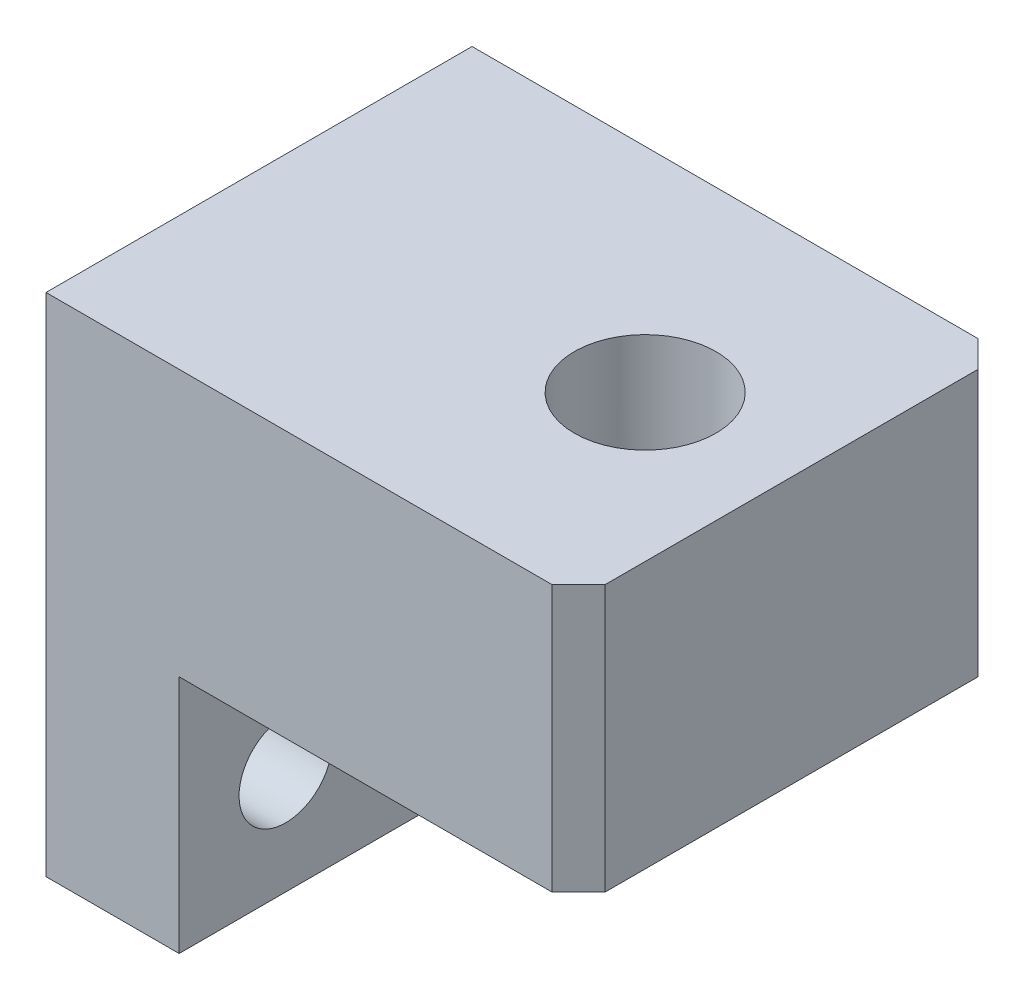
SolidWorks part; units mm, degrees
ref_plane "Front Plane" through (0, 0, 0) normal (0, 0, 1) x (1, 0, 0)
ref_plane "Top Plane" through (0, 0, 0) normal (0, 1, 0) x (1, 0, 0)
ref_plane "Right Plane" through (0, 0, 0) normal (1, 0, 0) x (0, 0, -1)
sketch "Sketch1" plane through (0, 0, 0) normal (0, 0, 1) x (1, 0, 0)
  line L0 (-8.5475, 7.8547) -> (11.4525, 7.8547)
  line L1 (11.4525, 7.8547) -> (11.4525, -2.1453)
  line L2 (11.4525, -2.1453) -> (-3.5475, -2.1453)
  line L3 (-3.5475, -2.1453) -> (-3.5475, -11.1453)
  line L4 (-3.5475, -11.1453) -> (-8.5475, -11.1453)
  line L5 (-8.5475, -11.1453) -> (-8.5475, 7.8547)
  point P3 (-8.2123, 3.2123)
  dimension "D1" = 20
  dimension "D2" = 19
  dimension "D3" = 10
  dimension "D4" = 15
extrude "Boss-Extrude1" add sketch "Sketch1" along normal blind 16
sketch "Sketch2" plane through (0, 7.8547, 0) normal (0, 1, 0) x (1, 0, 0)
  line L0 (11.4525, -16) -> (-8.5475, -16) construction
  line L1 (-8.5475, -16) -> (-8.5475, 0) construction
  circle A0 centre (5.9525, -8) radius 2.658
  dimension "D1" = 8
  dimension "D2" = 14.5
extrude "Cut-Extrude1" cut sketch "Sketch2" against normal blind 16
sketch "Sketch3" plane through (-3.5475, 0, 0) normal (1, 0, 0) x (0, 0, -1)
  line L1 (0, 7.8547) -> (0, -11.1453) construction
  line L2 (-16, -11.1453) -> (0, -11.1453) construction
  circle A0 centre (-12, -7.1453) radius 1.75
  circle A1 centre (-4, -7.1453) radius 1.75
  point P8 (0, 0)
  dimension "D1" = 8
  dimension "D2" = 3.5
  dimension "D3" = 4
  dimension "D4" = 4
extrude "Cut-Extrude2" cut sketch "Sketch3" against normal up to vertex (5 mm away)
chamfer "Chamfer1" distance 1 angle 45 2 edges at (11.4525, 2.8547, 16) (11.4525, 2.8547, 0)
